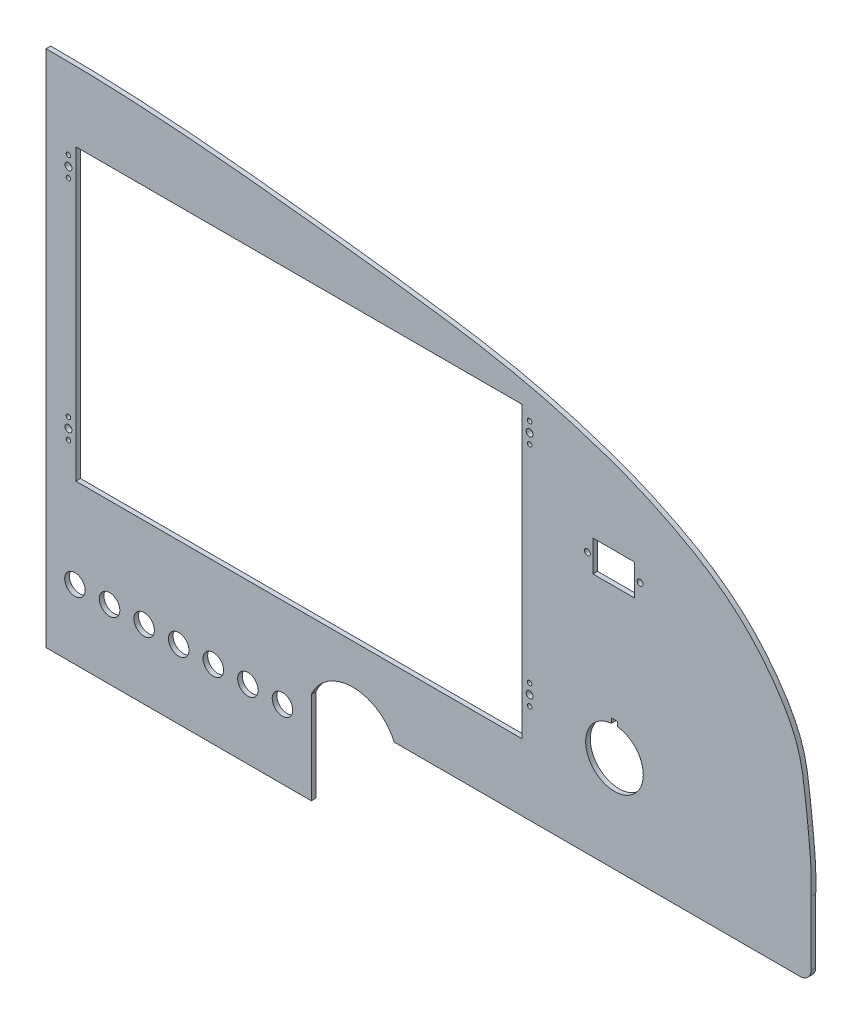
SolidWorks part; units mm, degrees
ref_plane "Front Plane" through (0, 0, 0) normal (0, 0, 1) x (1, 0, 0)
ref_plane "Top Plane" through (0, 0, 0) normal (0, 1, 0) x (1, 0, 0)
ref_plane "Right Plane" through (0, 0, 0) normal (1, 0, 0) x (0, 0, -1)
sketch "Sketch1" plane through (0, 0, 0) normal (0, 0, 1) x (1, 0, 0)
  line L0 (96.0293, -57.314) -> (242.0793, -57.314)
  line L1 (242.0793, -57.314) -> (242.0793, -6.514)
  line L2 (-194.2778, -401.0635) -> (-194.2778, 1298.9365) construction
  line L3 (-480.7083, -13.8992) -> (-243.8145, -13.8992) construction
  line L4 (270.5665, 103.4842) -> (354.2964, 121.2698) construction
  line L6 (287.7993, -6.514) -> (490.9993, -6.514)
  line L7 (96.0293, -57.314) -> (96.0293, 228.436)
  line L8 (96.0293, 228.436) -> (97.0023, 228.436)
  line L9 (517.3817, 34.6926) -> (517.3817, -0.418)
  line L10 (511.2857, -6.514) -> (490.9993, -6.514)
  arc A0 (517.3817, -0.418) -> (511.2857, -6.514) centre (511.2857, -0.418) cw
  arc A1 (242.0793, -6.514) -> (287.7993, -6.514) centre (264.9393, -16.6596) cw
  spline S0 degree 3 poles (96.0293, 228.436) (144.9267, 228.6583) (203.5486, 222.9755) (270.563, 215.2417) (301.0543, 211.3483) (337.4031, 206.2817) (371.2305, 199.1224) (398.5745, 190.6286) (416.4766, 184.4617) (436.8535, 175.4402) (458.3328, 163.9815) (480.8535, 146.8707) (498.4953, 125.9477) (511.7925, 102.3424) (513.9002, 82.9654) (515.1162, 71.7683) (515.4609, 68.7509) (515.686, 66.8487) knots 0 0 0 0 0.254671 0.306962 0.351943 0.415023 0.498429 0.531879 0.564371 0.597134 0.648058 0.691031 0.743912 0.78944 0.83209 0.837987 0.848415 0.848415 0.848415 0.848415
  spline S1 degree 3 poles (515.686, 66.8487) (516.9185, 56.1816) (517.794, 45.4402) (517.3817, 34.6926) knots 0 0 0 0 1 1 1 1
  line B0 (110.2276, 178.398) -> (112.3866, 178.398) construction
  line B1 (112.3866, 189.828) -> (358.2586, 189.828)
  line B2 (112.3866, 189.828) -> (112.3866, 30.316)
  line B3 (112.3866, 30.316) -> (358.2586, 30.316)
  line B4 (358.2586, 189.828) -> (358.2586, 30.316)
  line B5 (360.4176, 178.398) -> (358.2586, 178.398) construction
  line B6 (108.3226, 183.948) -> (108.3226, 178.398) construction
  line B7 (108.3226, 178.398) -> (108.3226, 172.848) construction
  line B8 (108.3226, 172.848) -> (108.3226, 178.398)
  line B9 (108.3226, 58.98) -> (108.3226, 53.43) construction
  line B10 (108.3226, 53.43) -> (108.3226, 47.88) construction
  line B11 (108.3226, 47.88) -> (108.3226, 53.43)
  line B12 (94.9876, 25.236) -> (94.9876, 194.908) construction
  line B13 (94.9876, 194.908) -> (375.6576, 194.908) construction
  line B14 (375.6576, 194.908) -> (375.6576, 25.236) construction
  line B15 (375.6576, 25.236) -> (94.9876, 25.236) construction
  line B16 (242.8815, 178.398) -> (245.0405, 178.398) construction
  line B17 (362.3226, 183.948) -> (362.3226, 178.398) construction
  line B18 (362.3226, 178.398) -> (362.3226, 172.848) construction
  line B19 (362.3226, 172.848) -> (362.3226, 178.398) construction
  line B20 (242.2702, 53.43) -> (244.4292, 53.43) construction
  line B21 (362.3226, 58.98) -> (362.3226, 53.43) construction
  line B22 (362.3226, 53.43) -> (362.3226, 47.88) construction
  line B23 (362.3226, 47.88) -> (362.3226, 53.43)
  circle B24 centre (362.3226, 178.398) radius 1.905
  circle B25 centre (108.3226, 178.398) radius 1.905
  circle B26 centre (108.3226, 53.43) radius 1.905
  circle B27 centre (362.3226, 53.43) radius 1.905
  circle B28 centre (108.3226, 183.948) radius 1.2446
  circle B29 centre (108.3226, 172.848) radius 1.2446
  circle B30 centre (108.3226, 58.98) radius 1.2446
  circle B31 centre (108.3226, 47.88) radius 1.2446
  circle B32 centre (362.3226, 183.948) radius 1.2446
  circle B33 centre (362.3226, 172.848) radius 1.2446
  circle B34 centre (362.3226, 58.98) radius 1.2446
  circle B35 centre (362.3226, 47.88) radius 1.2446
  dimension "D5" = 85.598
  dimension "D6" = 45.72
  dimension "D7" = 45.72
  dimension "D8" = 36.83
  dimension "D9" = 6.096
  dimension "D1" = 285.75
  dimension "D2" = 146.05
  dimension "D3" = 50.8
  dimension "D4" = 203.2
sketch_block_instance "HDX Block-4"
sketch_block "HDX Block" parameters "D1"=3.81, "D11"=2.4892, "D13"=2.4892, "D15"=2.4892, "D18"=2.4892, "D2"=124.968, "D3"=11.43, "D4"=159.512, "D5"=245.872, "D6"=254, "D7"=280.67, "D8"=169.672, "D9"=5.08, "D10"=17.399, "D12"=11.1, "D14"=11.1, "D16"=11.1, "D17"=5.55, "D19"=11.1, "D20"=5.55, "D21"=5.08
extrude "Boss-Extrude1" add sketch "Sketch1" along normal blind 2.54
sketch "Sketch2" plane through (0, 0, 2.54) normal (0, 0, 1) x (1, 0, 0)
  line L0 (407.4137, 64.8582) -> (407.4137, 62.3182)
  line L1 (242.0793, -57.314) -> (242.0793, -6.514) construction
  line L2 (96.0293, -57.314) -> (96.0293, 228.436) construction
  line L3 (96.0293, -57.314) -> (96.0293, 228.436)
  line L4 (242.0793, -57.314) -> (242.0793, -6.514)
  line L5 (407.4137, 64.8582) -> (410.7157, 64.8582)
  line L6 (410.7157, 64.8582) -> (410.7157, 62.3182)
  line L7 (407.4137, 62.3182) -> (410.7157, 62.3182)
  circle A0 centre (111.9043, -19.214) radius 5.6515
  circle A1 centre (130.9543, -19.214) radius 5.6515
  circle A2 centre (150.0043, -19.214) radius 5.6515
  circle A3 centre (169.0543, -19.214) radius 5.6515
  circle A4 centre (188.1043, -19.214) radius 5.6515
  circle A5 centre (207.1543, -19.214) radius 5.6515
  circle A6 centre (226.2043, -19.214) radius 5.6515
  circle A7 centre (409.0647, 46.5293) radius 15.875
  point P0 (111.9043, -19.214)
  point P1 (130.9543, -19.214)
  point P2 (150.0043, -19.214)
  point P3 (169.0543, -19.214)
  point P4 (188.1043, -19.214)
  point P5 (207.1543, -19.214)
  point P18 (242.0793, -19.214)
  point P19 (409.0647, 62.4043)
  point P24 (226.2043, -19.214)
  point P33 (409.0647, 62.3182)
  dimension "D6" = 11.303
  dimension "D9" = 31.75
  dimension "D1" = 19.05
  dimension "D2" = 19.05
  dimension "D3" = 19.05
  dimension "D4" = 19.05
  dimension "D5" = 19.05
  dimension "D7" = 19.05
  dimension "D8" = 38.1
  dimension "D10" = 2.54
  dimension "D11" = 3.302
extrude "Cut-Extrude2" cut sketch "Sketch2" against normal through all contours A0 | A1 | A2 | A3 | A4 | A5 | A6 | A7 | L7 L6 L5 L0
sketch "Sketch3" plane through (0, 0, 0) normal (0, 0, 1) x (1, 0, 0)
  line B0 (394.1543, 137.3039) -> (397.1642, 137.3039) construction
  line B1 (397.1642, 128.4532) -> (397.1642, 145.5982)
  line B2 (397.1642, 128.4532) -> (420.1512, 128.4532)
  line B3 (420.1512, 128.4532) -> (420.1512, 145.5982)
  line B4 (397.1642, 145.5982) -> (420.1512, 145.5982)
  line B5 (423.1611, 137.3039) -> (420.1512, 137.3039) construction
  circle B6 centre (394.1543, 137.3039) radius 1.6319
  circle B7 centre (423.1611, 137.3039) radius 1.6319
sketch_block_instance "USB Block-3"
sketch_block "USB Block" parameters "D3"=3.2639, "D1"=17.145, "D2"=22.987, "D4"=3.0099, "D5"=8.2943
extrude "Cut-Extrude5" cut sketch "Sketch3" against normal through all and the other way through all
